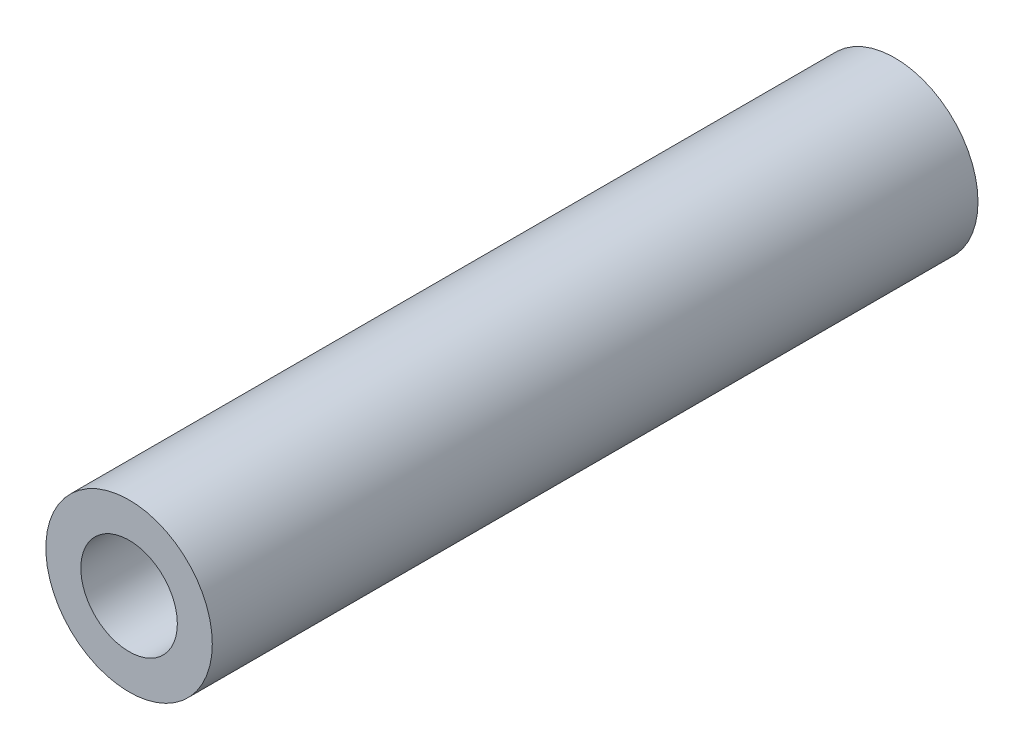
SolidWorks part; units mm, degrees
ref_plane "前视基准面" through (0, 0, 0) normal (0, 0, 1) x (1, 0, 0)
ref_plane "上视基准面" through (0, 0, 0) normal (0, 1, 0) x (1, 0, 0)
ref_plane "右视基准面" through (0, 0, 0) normal (1, 0, 0) x (0, 0, -1)
sketch "草图1" plane through (0, 0, 0) normal (0, 0, 1) x (1, 0, 0)
  circle A0 centre (0, 0) radius 1.45
  circle A1 centre (0, 0) radius 2.5
extrude "凸台-拉伸1" add sketch "草图1" along normal blind 23
